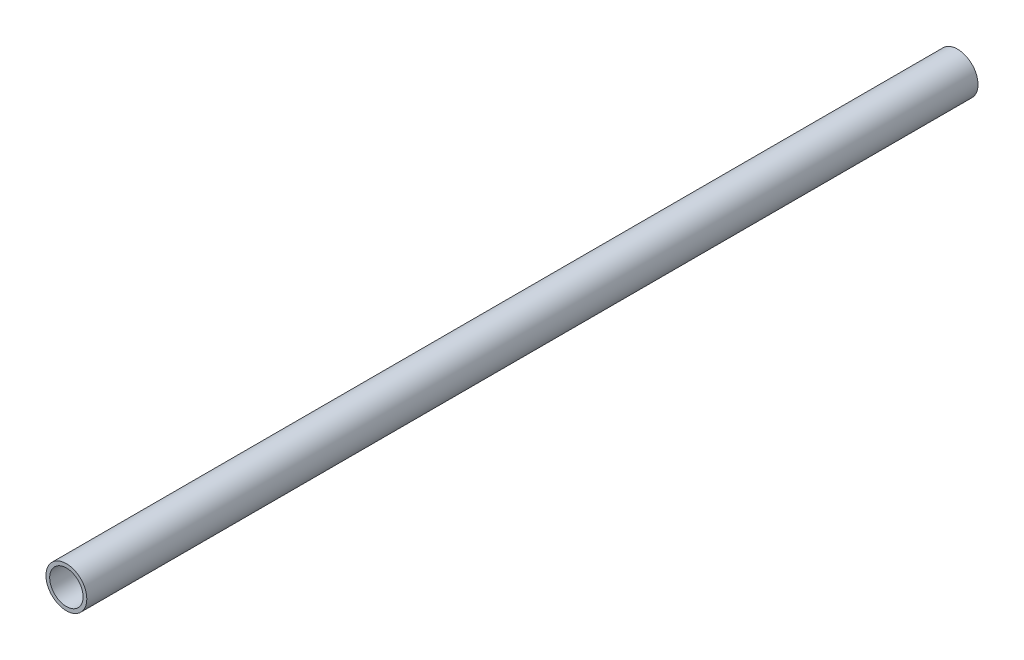
SolidWorks part; units mm, degrees
material "2014 合金"
ref_plane "前视基准面" through (0, 0, 0) normal (0, 0, 1) x (1, 0, 0)
ref_plane "上视基准面" through (0, 0, 0) normal (0, 1, 0) x (1, 0, 0)
ref_plane "右视基准面" through (0, 0, 0) normal (1, 0, 0) x (0, 0, -1)
other "Configuration Table"
sketch "草图1" plane through (0, 0, 0) normal (0, 0, 1) x (1, 0, 0)
  circle A0 centre (0, 0.0154) radius 5.5
  circle A1 centre (0, 0.0154) radius 4.5
  dimension "D1" = 11
  dimension "D2" = 9
extrude "凸台-拉伸1" add sketch "草图1" along normal blind 240
